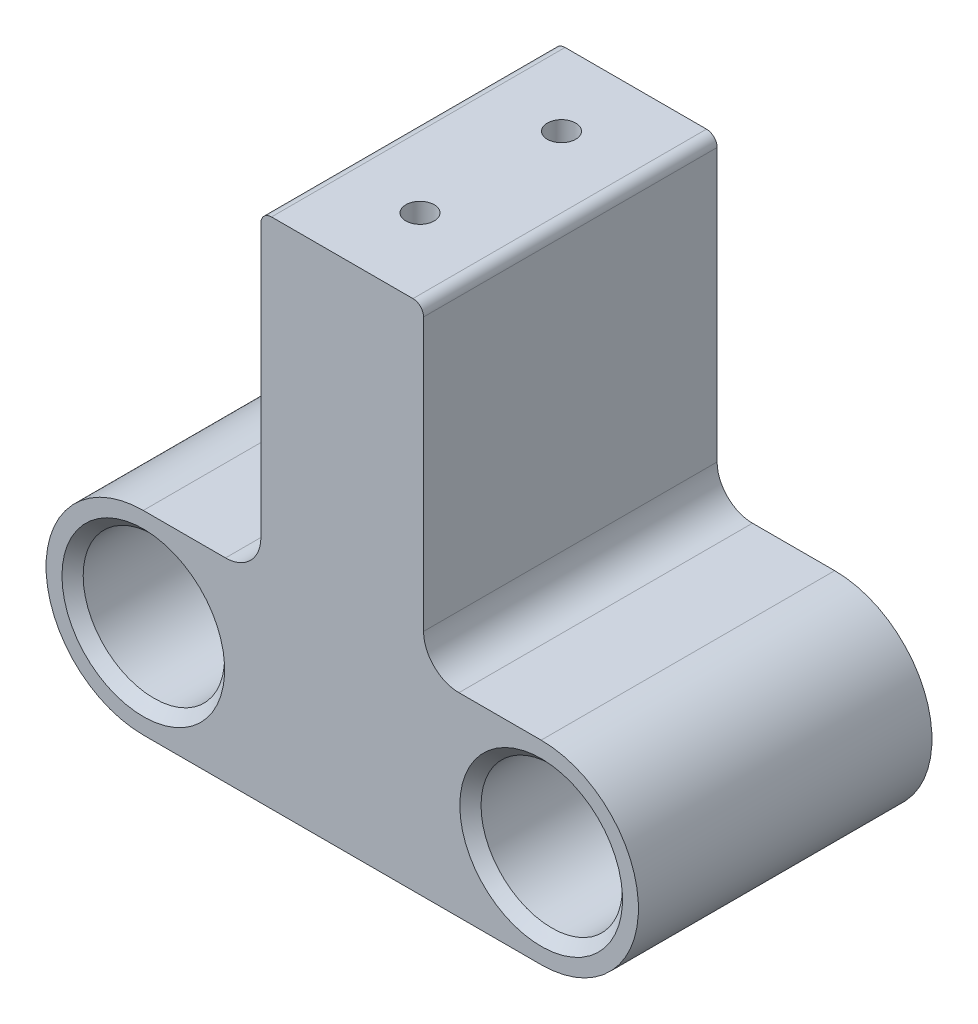
SolidWorks part; units mm, degrees
material "Delrin 2700 NC010, Low Viscosity Acetal Copolymer (SS)"
ref_plane "Front Plane" through (0, 0, 0) normal (0, 0, 1) x (1, 0, 0)
ref_plane "Top Plane" through (0, 0, 0) normal (0, 1, 0) x (1, 0, 0)
ref_plane "Right Plane" through (0, 0, 0) normal (1, 0, 0) x (0, 0, -1)
sketch "Sketch1" plane through (0, 0, 0) normal (0, 0, 1) x (1, 0, 0)
  line L0 (0, 22.0147) -> (0, -21.8158) construction
  line L3 (-5.842, 18.669) -> (-5.842, -1.651)
  line L4 (-5.842, 18.669) -> (5.842, 18.669)
  line L5 (5.842, 18.669) -> (5.842, -1.651)
  line L8 (28.575, -20.701) -> (-28.575, -20.701)
  line L9 (28.575, -20.701) -> (28.575, -1.651)
  line L10 (28.575, -1.651) -> (5.842, -1.651)
  line L11 (-28.575, -20.701) -> (-28.575, -1.651)
  line L12 (-5.842, -1.651) -> (-28.575, -1.651)
  circle A0 centre (14.2875, -11.176) radius 1.27
  circle A1 centre (-14.2875, -11.176) radius 1.27
  dimension "D4" = 2.54
  dimension "D5" = 2.54
  dimension "D1" = 19.05
  dimension "D2" = 5.842
  dimension "D3" = 5.842
  dimension "D6" = 28.575
  dimension "D7" = 14.2875
  dimension "D8" = 9.525
  dimension "D9" = 9.525
extrude "Boss-Extrude1" add sketch "Sketch1" along normal blind 25.4
hole_wizard "CSK for 1/4 Flat Head Machine Screw1" positions "Sketch3" profile "Sketch2" countersink size "1/4" standard "ANSI Inch" end condition through all
sketch "Sketch3" plane through (0, 0, 25.4) normal (0, 0, 1) x (1, 0, 0)
  circle A0 centre (-14.2875, -11.176) radius 1.27 construction
  circle A1 centre (14.2875, -11.176) radius 1.27 construction
  point P0 (-14.2875, -11.176)
  point P2 (14.2875, -11.176)
sketch "Sketch2" plane through (-14.2875, -11.176, 25.4) normal (1, 0, 0) x (0, -1, 0)
  line L0 (0, 0) -> (0, 25.4)
  line L1 (0, 25.4) -> (3.3782, 25.4)
  line L2 (3.3782, 25.4) -> (3.3782, 3.7749)
  line L3 (3.3782, 3.7749) -> (6.6597, 0)
  line L5 (6.6597, 0) -> (0, 0)
  line L6 (-3.3782, 3.7749) -> (-6.6597, 0) construction
  line L11 (0, -6.35) -> (0, 107.95) construction
  dimension "Thru Hole Dia." = 6.7564
  dimension "Thru Hole Depth" = 25.4
  dimension "Near C'Sink Dia." = 13.3194
  dimension "Near C'Sink Angle" = 82
sketch "Sketch4" plane through (0, 18.669, 0) normal (0, 1, 0) x (1, 0, 0)
  line L0 (0, 7.3941) -> (0, -24.3813) construction
  line L1 (33.9175, -10.414) -> (-38.6382, -10.414) construction
  line L2 (28.575, 0) -> (5.842, 0) construction
  circle A0 centre (0, -5.334) radius 1.016
  circle A1 centre (0, -15.494) radius 1.016
  dimension "D1" = 2.032
  dimension "D2" = 5.08
  dimension "D6" = 10.414
extrude "Cut-Extrude1" cut sketch "Sketch4" against normal through all
sketch "Sketch5" plane through (0, 18.669, 0) normal (0, 1, 0) x (1, 0, 0)
  line L0 (28.575, 0) -> (-28.575, 0) construction
  line L1 (-32.2349, -29.2552) -> (33.5033, -29.2552)
  line L2 (-32.2349, -29.2552) -> (-32.2349, -21.082)
  line L3 (-32.2349, -21.082) -> (33.5033, -21.082)
  line L4 (33.5033, -29.2552) -> (33.5033, -21.082)
  dimension "D1" = 21.082
extrude "Cut-Extrude2" cut sketch "Sketch5" against normal through all
fillet "Fillet1" radius 0.762 2 edges at (5.842, 18.669, 10.541) (-5.842, 18.669, 10.541)
sketch "Sketch8" plane through (0, 0, 21.082) normal (0, 0, 1) x (1, 0, 0)
  line L0 (28.575, -1.651) -> (28.575, -20.701) construction
  line L1 (37.1868, 0.7627) -> (23.495, 0.7627)
  line L2 (37.1868, 0.7627) -> (37.1868, -24.8731)
  line L3 (37.1868, -24.8731) -> (23.495, -24.8731)
  line L4 (23.495, 0.7627) -> (23.495, -24.8731)
  line L5 (-40.8768, 3.5787) -> (-23.495, 3.5787)
  line L6 (-40.8768, 3.5787) -> (-40.8768, -23.1252)
  line L7 (-40.8768, -23.1252) -> (-23.495, -23.1252)
  line L8 (-23.495, 3.5787) -> (-23.495, -23.1252)
  line L9 (-28.575, -20.701) -> (-28.575, -1.651) construction
  dimension "D1" = 5.08
  dimension "D2" = 5.08
extrude "Cut-Extrude3" cut sketch "Sketch8" against normal through all
sketch "Sketch9" plane through (0, 0, 21.082) normal (0, 0, 1) x (1, 0, 0)
  circle A0 centre (14.2875, -11.176) radius 5.08
  circle A1 centre (-14.2875, -11.176) radius 5.08
  dimension "D1" = 10.16
  dimension "D2" = 10.16
extrude "Cut-Extrude4" cut sketch "Sketch9" against normal offset from surface (11.557 mm away) 9.525
chamfer "Chamfer1" distance 0.762 angle 45 4 edges at (19.3675, -11.176, 21.082) (-9.2075, -11.176, 21.082) (0, -20.701, 6.35) (0, -20.701, 14.478)
sketch "Sketch10" plane through (0, -1.651, 0) normal (0, 1, 0) x (1, 0, 0)
  line L0 (5.842, -21.082) -> (5.842, 0) construction
  line L1 (-37.2448, 3.5874) -> (-5.842, 3.5874)
  line L2 (-37.2448, 3.5874) -> (-37.2448, -29.6616)
  line L3 (-37.2448, -29.6616) -> (-5.842, -29.6616)
  line L4 (-5.842, 3.5874) -> (-5.842, -29.6616)
  line L5 (32.0467, 2.715) -> (5.842, 2.715)
  line L6 (32.0467, 2.715) -> (32.0467, -26.7536)
  line L7 (32.0467, -26.7536) -> (5.842, -26.7536)
  line L8 (5.842, 2.715) -> (5.842, -26.7536)
  line L9 (-5.842, -21.082) -> (-5.842, 0) construction
extrude "Cut-Extrude5" cut sketch "Sketch10" against normal blind 2.54
sketch "Sketch11" plane through (0, 0, 21.082) normal (0, 0, 1) x (1, 0, 0)
  line L0 (23.495, -4.191) -> (5.842, -4.191) construction
  line L1 (-23.495, -4.191) -> (-5.842, -4.191) construction
  line L2 (-5.842, -4.191) -> (-5.842, 17.907) construction
  line L3 (14.2875, -4.191) -> (5.842, -4.191)
  line L5 (14.2875, -24.5244) -> (14.2875, 1.1151) construction
  line L6 (-14.2875, -23.2643) -> (-14.2875, -0.8721) construction
  line L7 (-25.3013, -26.4272) -> (26.2687, -26.4272)
  line L9 (14.2875, -18.161) -> (-14.2875, -18.161)
  line L10 (-14.2875, -4.191) -> (-5.842, -4.191)
  line L11 (-5.842, -4.191) -> (-5.842, 17.907)
  line L12 (5.842, 17.907) -> (5.842, -4.191) construction
  line L13 (5.842, 17.907) -> (5.842, -4.191)
  line L14 (-5.08, 18.669) -> (5.08, 18.669) construction
  line L15 (-5.08, 18.669) -> (5.08, 18.669)
  line L16 (-25.3013, -26.4272) -> (-25.3013, 22.9132)
  line L17 (-25.3013, 22.9132) -> (26.2687, 22.9132)
  line L18 (26.2687, -26.4272) -> (26.2687, 22.9132)
  arc A0 (-14.2875, -4.191) -> (-14.2875, -18.161) centre (-14.2875, -11.176) ccw
  arc A1 (14.2875, -18.161) -> (14.2875, -4.191) centre (14.2875, -11.176) ccw
  arc A2 (5.842, 17.907) -> (5.08, 18.669) centre (5.08, 17.907) ccw construction
  arc A3 (5.842, 17.907) -> (5.08, 18.669) centre (5.08, 17.907) ccw
  arc A4 (-5.08, 18.669) -> (-5.842, 17.907) centre (-5.08, 17.907) ccw construction
  arc A5 (-5.08, 18.669) -> (-5.842, 17.907) centre (-5.08, 17.907) ccw
extrude "Cut-Extrude6" cut sketch "Sketch11" against normal through all
fillet "Fillet3" radius 2.54 2 edges at (5.842, -4.191, 10.541) (-5.842, -4.191, 10.541)
